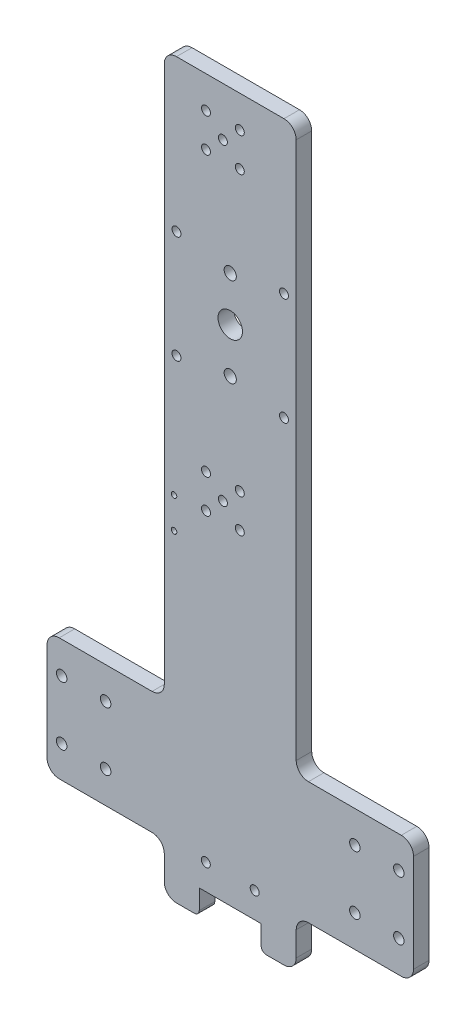
SolidWorks part; units mm, degrees
ref_plane "Front Plane" through (0, 0, 0) normal (0, 0, 1) x (1, 0, 0)
ref_plane "Top Plane" through (0, 0, 0) normal (0, 1, 0) x (1, 0, 0)
ref_plane "Right Plane" through (0, 0, 0) normal (1, 0, 0) x (0, 0, -1)
sketch "Sketch1" plane through (0, 0, 0) normal (0, 0, 1) x (1, 0, 0)
  line L0 (-27, 70) -> (-27, 300)
  line L1 (27, 20) -> (75, 20)
  line L2 (-27, 300) -> (27, 300)
  line L3 (27, 70) -> (27, 300)
  line L5 (27, 20) -> (27, 0)
  line L6 (27, 70) -> (75, 70)
  line L7 (-75, 70) -> (-27, 70)
  line L8 (-75, 70) -> (-75, 20)
  line L9 (-75, 20) -> (-27, 20)
  line L10 (75, 70) -> (75, 20)
  line L11 (27, 0) -> (-27, 0)
  line L12 (-27, 20) -> (-27, 0)
  point P1 (0, 0)
  dimension "D1" = 300
  dimension "D2" = 54
  dimension "D3" = 150
  dimension "D4" = 50
  dimension "D5" = 20
extrude "Boss-Extrude1" add sketch "Sketch1" along normal blind 6.35
fillet "Fillet1" radius 5 12 edges at (27, 300, 3.175) (-27, 300, 3.175) (75, 70, 3.175) (-75, 20, 3.175) (-75, 70, 3.175) (-27, 70, 3.175) (27, 70, 3.175) (27, 0, 3.175) (-27, 0, 3.175) (-27, 20, 3.175) (27, 20, 3.175) (75, 20, 3.175)
sketch "Sketch2" plane through (0, 0, 6.35) normal (0, 0, 1) x (1, 0, 0)
  line L0 (-3, 280) -> (-3, 152) construction
  line L1 (22, 300) -> (-22, 300) construction
  line L2 (-9.9148, 273.0852) -> (-9.9148, 286.9148) construction
  line L3 (-9.9148, 273.0852) -> (3.9148, 273.0852) construction
  line L4 (-9.9148, 286.9148) -> (3.9148, 286.9148) construction
  line L5 (3.9148, 273.0852) -> (3.9148, 286.9148) construction
  line L6 (-9.9148, 273.0852) -> (3.9148, 286.9148) construction
  line L7 (-9.9148, 286.9148) -> (3.9148, 273.0852) construction
  line L8 (-9.9148, 145.0852) -> (-9.9148, 158.9148) construction
  line L9 (-9.9148, 145.0852) -> (3.9148, 145.0852) construction
  line L10 (-9.9148, 158.9148) -> (3.9148, 158.9148) construction
  line L11 (3.9148, 145.0852) -> (3.9148, 158.9148) construction
  line L12 (-9.9148, 145.0852) -> (3.9148, 158.9148) construction
  line L13 (-9.9148, 158.9148) -> (3.9148, 145.0852) construction
  line L14 (-22, 194) -> (-22, 238) construction
  line L15 (-22, 194) -> (22, 194) construction
  line L16 (-22, 238) -> (22, 238) construction
  line L17 (22, 194) -> (22, 238) construction
  line L18 (-22, 194) -> (22, 238) construction
  line L19 (-22, 238) -> (22, 194) construction
  line L20 (0, 197.75) -> (0, 234.25) construction
  point P2 (-3, 216)
  point P3 (0, 216)
  point P7 (0, 216)
  point P22 (0, 216)
  dimension "D1" = 128
  dimension "D2" = 20
  dimension "D3" = 19.558
  dimension "D4" = 44
  dimension "D5" = 36.5
  dimension "D6" = 3
sketch "Sketch3" plane through (0, 0, 6.35) normal (0, 0, 1) x (1, 0, 0)
  circle A0 centre (0, 216) radius 5
  dimension "D1" = 10
extrude "Cut-Extrude1" cut sketch "Sketch3" against normal through all
hole_wizard "#6 Clearance Hole1" positions "Sketch5" profile "Sketch4" hole size "#6" standard "ANSI Inch" end condition through all
sketch "Sketch5" plane through (0, 0, 6.35) normal (0, 0, 1) x (1, 0, 0)
  point P0 (-22, 238)
  point P3 (-22, 194)
  point P6 (22, 194)
  point P9 (22, 238)
  point P12 (-9.9148, 273.0852)
  point P15 (-9.9148, 286.9148)
  point P18 (3.9148, 286.9148)
  point P21 (3.9148, 273.0852)
  point P24 (-9.9148, 158.9148)
  point P27 (3.9148, 158.9148)
  point P30 (3.9148, 145.0852)
  point P33 (-9.9148, 145.0852)
  point P36 (-3, 280)
  point P39 (-3, 152)
sketch "Sketch4" plane through (-22, 238, 6.35) normal (1, 0, 0) x (0, -1, 0)
  line L0 (0, 0) -> (0, 6.35)
  line L1 (0, 6.35) -> (1.8288, 6.35)
  line L2 (1.8288, 6.35) -> (1.8288, 0)
  line L5 (1.8288, 0) -> (0, 0)
  line L11 (0, -6.35) -> (0, 107.95) construction
  dimension "Thru Hole Dia." = 3.6576
  dimension "Thru Hole Depth" = 6.35
sketch "Sketch6" plane through (0, 0, 6.35) normal (0, 0, 1) x (1, 0, 0)
  line L0 (-12.7, 0) -> (-12.6, 10)
  line L2 (-12.6, 10) -> (12.6, 10)
  line L3 (12.6, 10) -> (12.7, 0)
  line L4 (12.7, 0) -> (-12.7, 0)
  point P2 (0, 10)
  point P3 (0, 0)
  point P4 (0, 0)
  dimension "D1" = 25.4
  dimension "D2" = 25.2
  dimension "D3" = 10
extrude "Cut-Extrude2" cut sketch "Sketch6" against normal through all
hole_wizard "#10 Clearance Hole2" positions "Sketch10" profile "Sketch9" hole size "#10" standard "ANSI Inch" end condition through all
sketch "Sketch10" plane through (0, 0, 6.35) normal (0, 0, 1) x (1, 0, 0)
  point P0 (0, 197.75)
  point P3 (0, 234.25)
sketch "Sketch9" plane through (0, 197.75, 6.35) normal (1, 0, 0) x (0, -1, 0)
  line L0 (0, 0) -> (0, 6.35)
  line L1 (0, 6.35) -> (2.4892, 6.35)
  line L2 (2.4892, 6.35) -> (2.4892, 0)
  line L5 (2.4892, 0) -> (0, 0)
  line L11 (0, -6.35) -> (0, 107.95) construction
  dimension "Thru Hole Dia." = 4.9784
  dimension "Thru Hole Depth" = 6.35
sketch "Sketch11" plane through (0, 0, 6.35) normal (0, 0, 1) x (1, 0, 0)
  line L0 (-10, 20.4648) -> (10, 20.4648) construction
  line L1 (12.6, 10) -> (-12.6, 10) construction
  point P2 (0, 20.4648)
  dimension "D1" = 20
  dimension "D2" = 10.4648
hole_wizard "#6 Clearance Hole2" positions "3DSketch1" profile "Sketch12" hole size "#6" standard "ANSI Inch" end condition through all
sketch3d "3DSketch1"
  point P0 (-10, 20.4648, 6.35)
  point P3 (10, 20.4648, 6.35)
sketch "Sketch12" plane through (-10, 20.4648, 6.35) normal (1, 0, 0) x (0, -1, 0)
  line L0 (0, 0) -> (0, 6.35)
  line L1 (0, 6.35) -> (1.8288, 6.35)
  line L2 (1.8288, 6.35) -> (1.8288, 0)
  line L5 (1.8288, 0) -> (0, 0)
  line L11 (0, -6.35) -> (0, 107.95) construction
  dimension "Thru Hole Dia." = 3.6576
  dimension "Thru Hole Depth" = 6.35
sketch "Sketch13" plane through (0, 0, 6.35) normal (0, 0, 1) x (1, 0, 0)
  line L0 (12.6, 10) -> (-12.6, 10) construction
  line L1 (51, 57) -> (69, 57) construction
  line L2 (51, 57) -> (51, 33) construction
  line L3 (51, 33) -> (69, 33) construction
  line L4 (69, 57) -> (69, 33) construction
  line L5 (51, 57) -> (69, 33) construction
  line L6 (51, 33) -> (69, 57) construction
  line L7 (75, 25) -> (75, 65) construction
  line L8 (60, 45) -> (-60, 45) construction
  line L9 (-51, 57) -> (-69, 57) construction
  line L10 (-51, 57) -> (-51, 33) construction
  line L11 (-51, 33) -> (-69, 33) construction
  line L12 (-69, 57) -> (-69, 33) construction
  line L13 (-51, 57) -> (-69, 33) construction
  line L14 (-51, 33) -> (-69, 57) construction
  point P0 (60, 45)
  point P12 (-60, 45)
  point P18 (0, 45)
  dimension "D1" = 18
  dimension "D2" = 24
  dimension "D3" = 35
  dimension "D4" = 15
hole_wizard "#8 Clearance Hole1" positions "3DSketch2" profile "Sketch14" hole size "#8" standard "ANSI Inch" end condition through all
sketch3d "3DSketch2"
  point P0 (51, 57, 6.35)
  point P3 (69, 57, 6.35)
  point P6 (69, 33, 6.35)
  point P9 (51, 33, 6.35)
  point P12 (-51, 57, 6.35)
  point P15 (-69, 57, 6.35)
  point P18 (-69, 33, 6.35)
  point P21 (-51, 33, 6.35)
sketch "Sketch14" plane through (51, 57, 6.35) normal (1, 0, 0) x (0, -1, 0)
  line L0 (0, 0) -> (0, 6.35)
  line L1 (0, 6.35) -> (2.1526, 6.35)
  line L2 (2.1526, 6.35) -> (2.1526, 0)
  line L5 (2.1526, 0) -> (0, 0)
  line L11 (0, -6.35) -> (0, 107.95) construction
  dimension "Thru Hole Dia." = 4.3053
  dimension "Thru Hole Depth" = 6.35
sketch "Sketch15" plane through (0, 0, 6.35) normal (0, 0, 1) x (1, 0, 0)
  line L0 (-23, 144.126) -> (-23, 131.426) construction
  point P2 (-3, 152)
  point P8 (-23, 137.776)
  dimension "D1" = 12.7
  dimension "D2" = 20
  dimension "D3" = 14.224
hole_wizard "Tap Drill for #4-40 Tap1" positions "3DSketch3" profile "Sketch16" hole size "#4-40" standard "ANSI Inch"
sketch3d "3DSketch3"
  point P0 (-23, 131.426, 6.35)
  point P3 (-23, 144.126, 6.35)
sketch "Sketch16" plane through (-23, 131.426, 6.35) normal (1, 0, 0) x (0, -1, 0)
  line L0 (0, 0) -> (0, 7.0292)
  line L1 (0, 7.0292) -> (1.1303, 6.35)
  line L2 (1.1303, 6.35) -> (1.1303, 0)
  line L5 (1.1303, 0) -> (0, 0)
  line L10 (0, 7.0292) -> (-1.1303, 6.35) construction
  line L11 (0, -6.35) -> (0, 107.95) construction
  dimension "Hole Dia." = 2.2606
  dimension "Hole Depth" = 6.35
  dimension "Drill Angle" = 118
fillet "Fillet2" radius 2 2 edges at (-12.7, 0, 3.175) (12.7, 0, 3.175)
